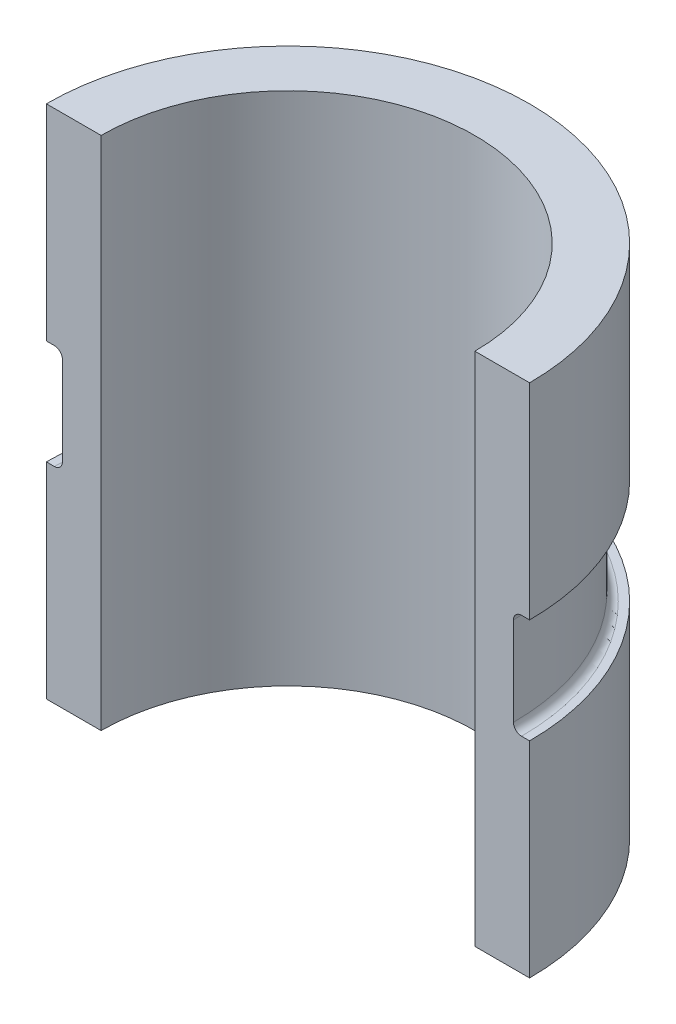
SolidWorks part; units mm, degrees
ref_plane "Front Plane" through (0, 0, 0) normal (0, 0, 1) x (1, 0, 0)
ref_plane "Top Plane" through (0, 0, 0) normal (0, 1, 0) x (1, 0, 0)
ref_plane "Right Plane" through (0, 0, 0) normal (1, 0, 0) x (0, 0, -1)
sketch "Sketch1" plane through (0, 0, 0) normal (0, 1, 0) x (1, 0, 0)
  line L0 (-29.464, 0) -> (-38.1, 0)
  line L1 (29.464, 0) -> (38.1, 0)
  arc A0 (-38.1, 0) -> (38.1, 0) centre (0, 0) cw
  arc A1 (-29.464, 0) -> (29.464, 0) centre (0, 0) cw
  dimension "D1" = 29.464
  dimension "D2" = 38.1
extrude "Boss-Extrude1" add sketch "Sketch1" along normal blind 81.28 contours A0 L1 A1 L0
sketch "Sketch2" plane through (0, 0, 0) normal (0, 0, 1) x (1, 0, 0)
  line L0 (-38.1, 48.895) -> (-35.56, 48.895)
  line L1 (-38.1, 81.28) -> (-38.1, 0) construction
  line L2 (-35.56, 48.895) -> (-35.56, 32.385)
  line L3 (-35.56, 32.385) -> (-38.1, 32.385)
  line L4 (-38.1, 32.385) -> (-38.1, 48.895)
  point P4 (-38.1, 40.64)
  dimension "D1" = 16.51
  dimension "D2" = 2.54
ref_axis "Axis1" through (0, 0, 0) along (0, 1, 0)
revolve "Cut-Revolve1" cut sketch "Sketch2" angle 180 about axis through (0, 0, 0) along (0, 1, 0)
fillet "Fillet1" radius 1.27 2 edges at (0, 48.895, -35.56) (0, 32.385, -35.56)
